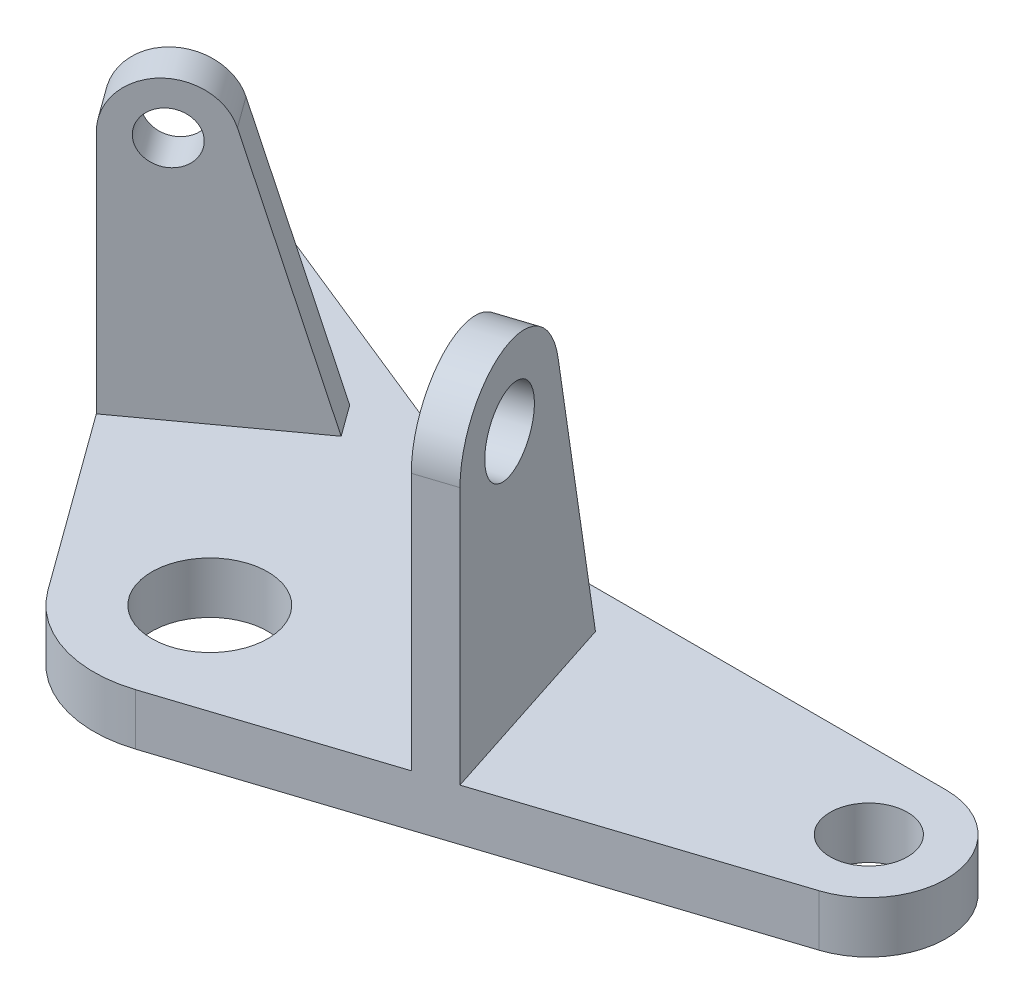
SolidWorks part; units mm, degrees
ref_plane "Front Plane" through (0, 0, 0) normal (0, 0, 1) x (1, 0, 0)
ref_plane "Top Plane" through (0, 0, 0) normal (0, 1, 0) x (1, 0, 0)
ref_plane "Right Plane" through (0, 0, 0) normal (1, 0, 0) x (0, 0, -1)
sketch "Sketch1" plane through (0, 0, 0) normal (0, 1, 0) x (1, 0, 0)
  line L0 (82, 32.3346) -> (14.7359, 32.3346)
  line L1 (85.7082, 8.922) -> (5.5623, -17.119)
  line L2 (14.7359, 32.3346) -> (-45.0031, 56.4708)
  line L3 (-54.4721, 44.351) -> (-14.5623, -10.5801)
  circle A0 centre (0, 0) radius 9
  circle A1 centre (82, 20.3346) radius 6
  circle A2 centre (-48, 49.0533) radius 4
  arc A3 (-45.0031, 56.4708) -> (-54.4721, 44.351) centre (-48, 49.0533) ccw
  arc A4 (85.7082, 8.922) -> (82, 32.3346) centre (82, 20.3346) ccw
  arc A5 (-14.5623, -10.5801) -> (5.5623, -17.119) centre (0, 0) ccw
  point P17 (0, 0)
  dimension "D1" = 18
  dimension "D3" = 12
  dimension "D5" = 8
  dimension "D6" = 36
  dimension "D7" = 16
  dimension "D8" = 24
  dimension "D2" = 82
  dimension "D4" = 48
  dimension "D9" = 18
  dimension "D10" = 22
  dimension "D11" = 54
extrude "Boss-Extrude1" add sketch "Sketch1" along normal blind 8
sketch "Sketch2" plane through (0, 8, 0) normal (0, 1, 0) x (1, 0, 0)
  line L0 (40.7514, -5.6854) -> (37.0841, 5.6013) construction
  line L1 (5.5623, -17.119) -> (85.7082, 8.922) construction
  line L2 (-36.3104, 19.3535) -> (-28.724, 24.8653) construction
  line L3 (-54.4721, 44.351) -> (-14.5623, -10.5801) construction
  dimension "D1" = 37
  dimension "D2" = 37
ref_plane "Plane1" through (-21.7481, 0, -29.9336) normal (0.5878, 0, 0.809) x (0.809, 0, -0.5878)
ref_plane "Plane2" through (35.1891, 0, -11.4336) normal (0.9511, 0, -0.309) x (-0.309, 0, -0.9511)
sketch "Sketch3" plane through (-21.7481, 0, -29.9336) normal (0.5878, 0, 0.809) x (0.809, 0, -0.5878)
  line L0 (-18, 8) -> (-18, 46)
  line L1 (-18, 46) -> (-18, 8)
  line L2 (-18, 8) -> (9.2187, 8)
  line L3 (-5.5623, 8) -> (74.5836, 8) construction
  line L4 (9.2187, 8) -> (-2.3099, 48.2051)
  line L5 (-18, 0) -> (-5.5623, 0) construction
  circle A0 centre (-10, 46) radius 8
  circle A1 centre (-10, 46) radius 4
  dimension "D2" = 16
  dimension "D4" = 8
  dimension "D1" = 74
  dimension "D3" = 46
extrude "Boss-Extrude2" add sketch "Sketch3" along normal mid plane 6 contours A0 L0 L2 L4 | A0 A1
sketch "Sketch5" plane through (35.1891, 0, -11.4336) normal (0.9511, 0, -0.309) x (-0.309, 0, -0.9511)
  line L0 (-18, 8) -> (-18, 48)
  line L1 (-18, 48) -> (-18, 8)
  line L2 (-18, 8) -> (14.7703, 8)
  line L3 (14.7703, 8) -> (5.7378, 50.4949)
  line L4 (-18, 8) -> (5.4127, 8) construction
  circle A0 centre (-6, 48) radius 12
  circle A1 centre (-6, 48) radius 6
  dimension "D2" = 24
  dimension "D3" = 12
  dimension "D1" = 78
extrude "Boss-Extrude3" add sketch "Sketch5" along normal mid plane 6 contours A0 L0 L2 L3 | A0 A1
fillet "Fillet1" radius 42 1 edges at (14.7359, 4, -32.3346)
